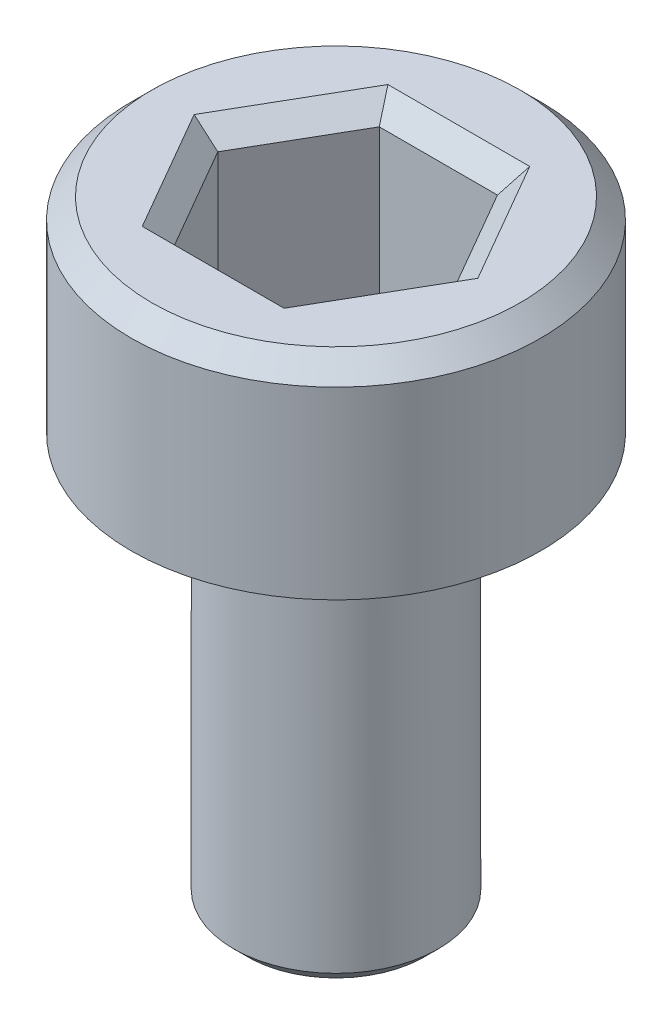
SolidWorks part; units mm, degrees
ref_plane "Front Plane" through (0, 0, 0) normal (0, 0, 1) x (1, 0, 0)
ref_plane "Top Plane" through (0, 0, 0) normal (0, 1, 0) x (1, 0, 0)
ref_plane "Right Plane" through (0, 0, 0) normal (1, 0, 0) x (0, 0, -1)
sketch "Sketch1" plane through (0, 0, 0) normal (0, 1, 0) x (1, 0, 0)
  circle A0 centre (0, 0) radius 3
  dimension "D1" = 6
extrude "Boss-Extrude1" add sketch "Sketch1" along normal blind 3
chamfer "Chamfer1" distance 0.3 angle 45 1 edges at (0, 3, 3)
sketch "Sketch2" plane through (0, 3, 0) normal (0, 1, 0) x (1, 0, 0)
  line L1 (1.7321, 0) -> (0.866, 1.5)
  line L2 (0.866, 1.5) -> (-0.866, 1.5)
  line L3 (-0.866, 1.5) -> (-1.7321, 0)
  line L4 (-1.7321, 0) -> (-0.866, -1.5)
  line L5 (-0.866, -1.5) -> (0.866, -1.5)
  line L6 (0.866, -1.5) -> (1.7321, 0)
  circle A0 centre (0, 0) radius 1.5 construction
  dimension "D1" = 3
extrude "Cut-Extrude1" cut sketch "Sketch2" against normal blind 2.5
chamfer "Chamfer2" distance 0.3 angle 45 6 edges at (1.299, 3, -0.75) (1.299, 3, 0.75) (0, 3, 1.5) (-1.299, 3, 0.75) (-1.299, 3, -0.75) (0, 3, -1.5)
sketch "Sketch3" plane through (0, 0, 0) normal (0, -1, 0) x (1, 0, 0)
  circle A0 centre (0, 0) radius 1.5
  dimension "D1" = 3
extrude "Boss-Extrude2" add sketch "Sketch3" along normal blind 6
chamfer "Chamfer3" distance 0.2 angle 45 1 edges at (0, -6, -1.5)
